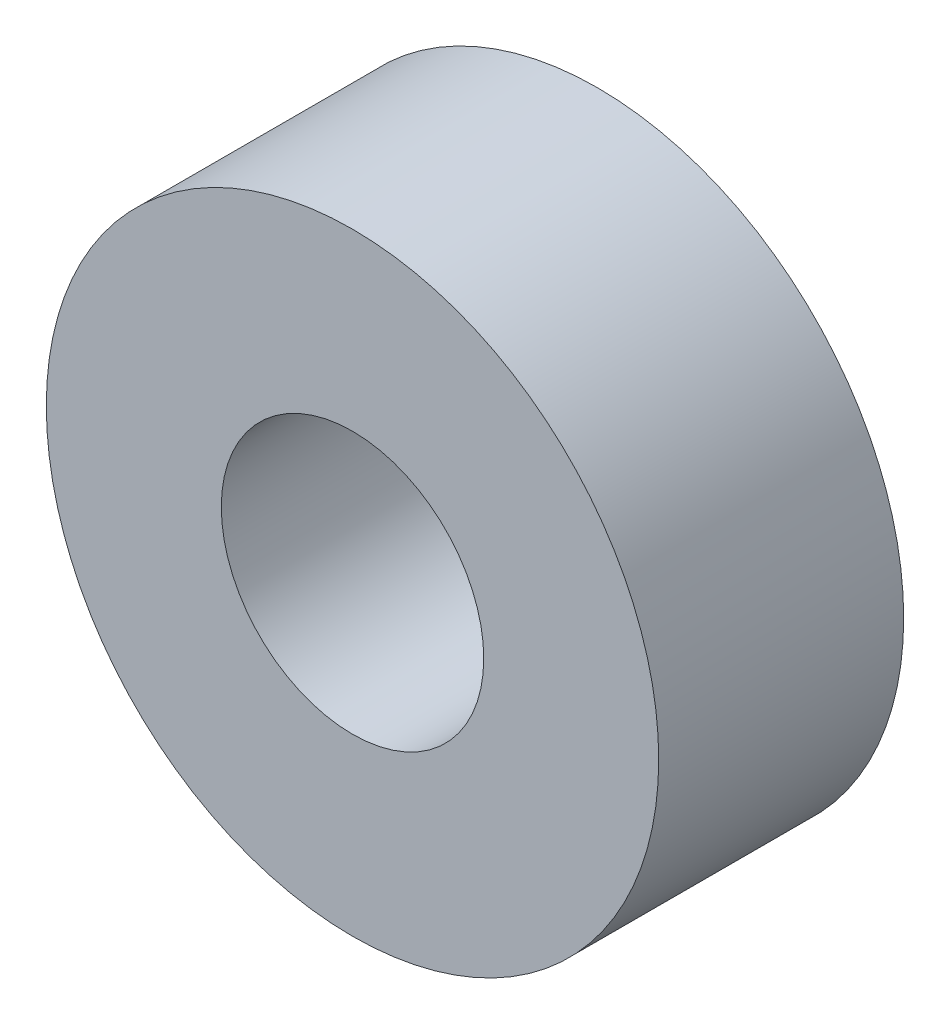
SolidWorks part; units mm, degrees
ref_plane "Alzado" through (0, 0, 0) normal (0, 0, 1) x (1, 0, 0)
ref_plane "Planta" through (0, 0, 0) normal (0, 1, 0) x (1, 0, 0)
ref_plane "Vista lateral" through (0, 0, 0) normal (1, 0, 0) x (0, 0, -1)
sketch "Croquis1" plane through (0, 0, 0) normal (0, 0, 1) x (1, 0, 0)
  circle A0 centre (0, 0) radius 7.5
  circle A1 centre (0, 0) radius 17.5
  dimension "D1" = 15
  dimension "D2" = 35
extrude "Saliente-Extruir1" add sketch "Croquis1" along normal blind 14
